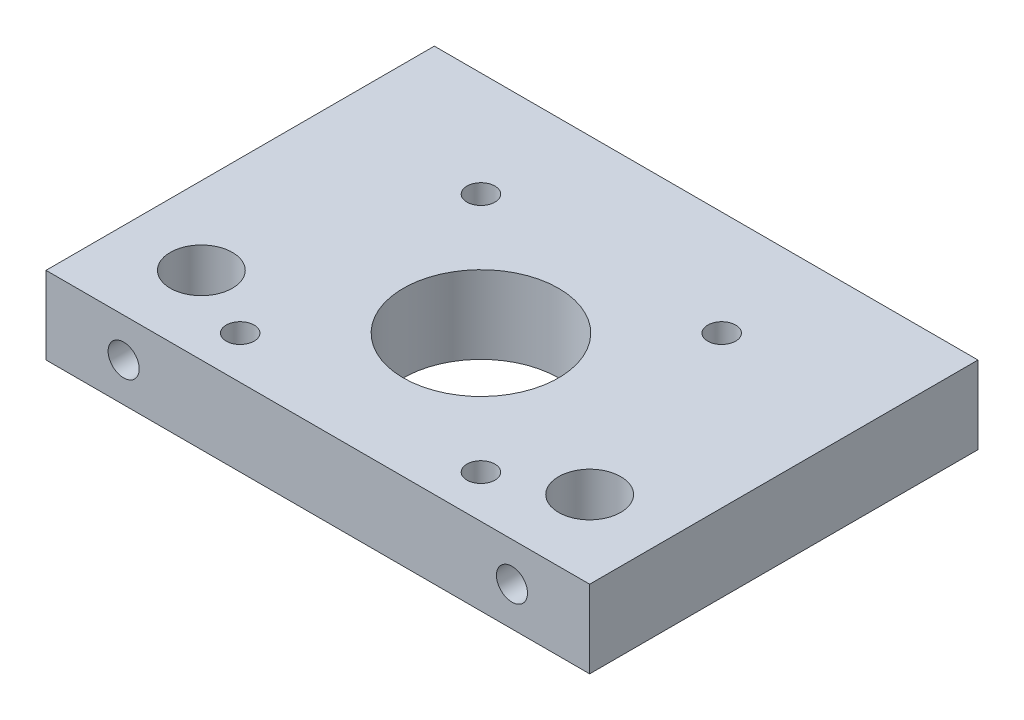
SolidWorks part; units mm, degrees
ref_plane "Front Plane" through (0, 0, 0) normal (0, 0, 1) x (1, 0, 0)
ref_plane "Top Plane" through (0, 0, 0) normal (0, 1, 0) x (1, 0, 0)
ref_plane "Right Plane" through (0, 0, 0) normal (1, 0, 0) x (0, 0, -1)
sketch "Sketch2" plane through (0, 0, 0) normal (0, 1, 0) x (1, 0, 0)
  line L1 (35, -25) -> (-35, -25)
  line L2 (35, -25) -> (35, 25)
  line L3 (35, 25) -> (-35, 25)
  line L4 (-35, -25) -> (-35, 25)
  line L5 (35, -25) -> (-35, 25) construction
  line L6 (35, 25) -> (-35, -25) construction
  point P0 (0, 0)
  dimension "D1" = 50
  dimension "D2" = 70
extrude "Boss-Extrude1" add sketch "Sketch2" along normal blind 10
sketch "Sketch3" plane through (0, 10, 0) normal (0, 1, 0) x (1, 0, 0)
  line L0 (0, 35) -> (0, -25) construction
  line L1 (-35, -25) -> (35, -25) construction
  line L2 (-35, 25) -> (-35, -25) construction
  circle A0 centre (-25, -15) radius 4
  circle A1 centre (25, -15) radius 4
  dimension "D4" = 8
  dimension "D1" = 10
  dimension "D2" = 10
  dimension "D3" = 50
extrude "Cut-Extrude1" cut sketch "Sketch3" against normal through all
sketch "Sketch4" plane through (0, 0, 0) normal (0, -1, 0) x (1, 0, 0)
  circle A0 centre (-15.5, 19.5) radius 1.8 construction
  circle A1 centre (-15.5, -11.5) radius 1.8 construction
  circle A2 centre (15.5, -11.5) radius 1.8 construction
  circle A3 centre (15.5, 19.5) radius 1.8 construction
  circle A4 centre (-15.5, 19.5) radius 1.8
  circle A5 centre (-15.5, -11.5) radius 1.8
  circle A6 centre (15.5, -11.5) radius 1.8
  circle A7 centre (15.5, 19.5) radius 1.8
extrude "Cut-Extrude2" cut sketch "Sketch4" against normal through all
sketch "Sketch5" plane through (0, 0, 0) normal (0, -1, 0) x (1, 0, 0)
  circle A0 centre (0, 4) radius 11 construction
  circle A1 centre (0, 4) radius 11
  circle A2 centre (0, 4) radius 10
  dimension "D1" = 20
extrude "Cut-Extrude3" cut sketch "Sketch5" against normal through all contours A2
sketch "Sketch6" plane through (0, 0, 25) normal (0, 0, 1) x (1, 0, 0)
  line L0 (0, 10) -> (0, 0) construction
  line L1 (-35, 10) -> (35, 10) construction
  line L2 (-35, 0) -> (35, 0) construction
  line L3 (0, 5) -> (35, 5) construction
  line L4 (35, 10) -> (35, 0) construction
  circle A0 centre (25, 5) radius 2
  circle A1 centre (-25, 5) radius 2
  dimension "D1" = 4
  dimension "D2" = 10
extrude "Cut-Extrude5" cut sketch "Sketch6" against normal blind 10
